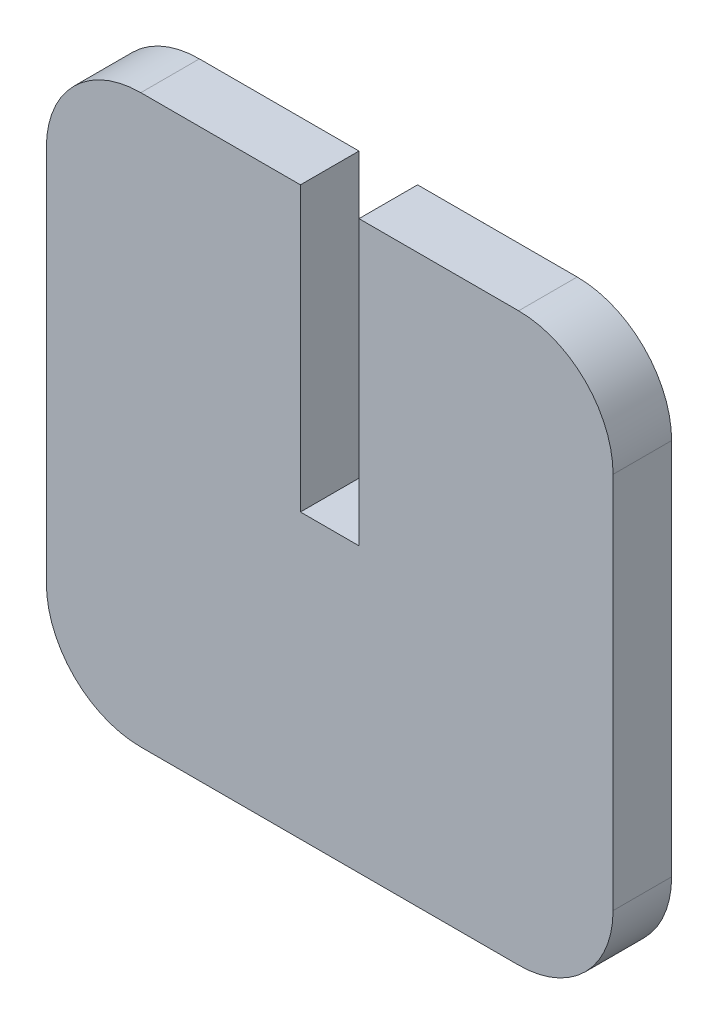
SolidWorks part; units mm, degrees
material "Teak"
ref_plane "Front Plane" through (0, 0, 0) normal (0, 0, 1) x (1, 0, 0)
ref_plane "Top Plane" through (0, 0, 0) normal (0, 1, 0) x (1, 0, 0)
ref_plane "Right Plane" through (0, 0, 0) normal (1, 0, 0) x (0, 0, -1)
sketch "Sketch1" plane through (0, 0, 0) normal (0, 0, 1) x (1, 0, 0)
  line L1 (-15, -15) -> (15, -15)
  line L2 (-15, -15) -> (-15, 15)
  line L3 (-15, 15) -> (15, 15)
  line L4 (15, -15) -> (15, 15)
  line L5 (-15, -15) -> (15, 15) construction
  line L6 (-15, 15) -> (15, -15) construction
  point P0 (0, 0)
  dimension "D1" = 30
  dimension "D2" = 30
extrude "Boss-Extrude1" add sketch "Sketch1" along normal blind 3.1
sketch "Sketch2" plane through (0, 15, 0) normal (0, 1, 0) x (1, 0, 0)
  line L0 (0, 0) -> (0, -3.1) construction
  line L1 (15, -3.1) -> (-15, -3.1) construction
  line L2 (15, 0) -> (-15, 0) construction
  line L3 (15, -3.1) -> (15, 0) construction
  line L4 (15, -1.55) -> (-15, -1.55) construction
  line L5 (-15, -3.1) -> (-15, 0) construction
  line L6 (-1.55, -3.1) -> (1.55, -3.1)
  line L7 (-1.55, -3.1) -> (-1.55, 0)
  line L8 (-1.55, 0) -> (1.55, 0)
  line L9 (1.55, -3.1) -> (1.55, 0)
  line L10 (-1.55, -3.1) -> (1.55, 0) construction
  line L11 (-1.55, 0) -> (1.55, -3.1) construction
  point P11 (0, -1.55)
  dimension "D1" = 3.1
extrude "Cut-Extrude1" cut sketch "Sketch2" against normal blind 15
fillet "Fillet1" radius 5 4 edges at (15, -15, 1.55) (15, 15, 1.55) (-15, -15, 1.55) (-15, 15, 1.55)
equation "\"p\"= 20mm"
equation "\"m\"= 1"
equation "\"hole_diam\"= 4mm"
equation "\"len_grip_1\" = 50mm"
equation "\"len_grip_2\" = 50mm"
equation "\"thick\" = 3.1mm"
equation "\"thick2\" = 20mm"
equation "\"wrist_cont_bearing_diam\"=3in"
equation "\"wrist_cont_bearing_thick\"=5/16in"
equation "\"len_forearm\" = 300mm"
equation "\"wrist_bearing_diam\"=3in"
equation "\"len_link\" = 7cm"
equation "\"elbow_cont_bearing_diam\"=10cm"
equation "\"elbow_cont_bearing2_diam\"=7.5cm"
equation "\"small_bearing_outer\"=13mm"
equation "\"servo1_L\"=40.7mm"
equation "\"servo1_W\"=20.5mm"
equation "\"servo1_H\"=43.5mm"
equation "\"servo1_hL\"=49mm"
equation "\"servo1_hW\"=10mm"
equation "\"D1@Sketch2\"=\"thick\""
equation "\"D1@Boss-Extrude1\"=\"thick\""
